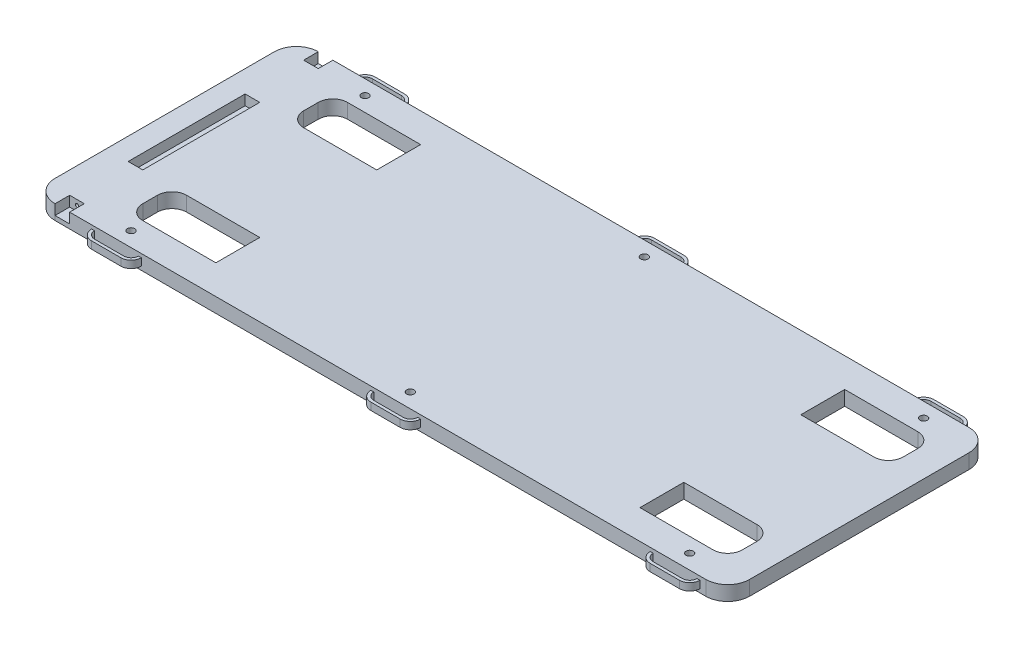
SolidWorks part; units mm, degrees
ref_plane "Front Plane" through (0, 0, 0) normal (0, 0, 1) x (1, 0, 0)
ref_plane "Top Plane" through (0, 0, 0) normal (0, 1, 0) x (1, 0, 0)
ref_plane "Right Plane" through (0, 0, 0) normal (1, 0, 0) x (0, 0, -1)
sketch "Main Body" plane through (0, 0, 0) normal (0, 1, 0) x (1, 0, 0)
  line L0 (-301.625, -95.25) -> (-301.625, 95.25)
  line L1 (-282.575, 114.3) -> (282.575, 114.3)
  line L2 (-282.575, -114.3) -> (282.575, -114.3)
  line L3 (301.625, 95.25) -> (301.625, -95.25)
  line L4 (-301.625, 0) -> (301.625, 0) construction
  arc A0 (-301.625, 95.25) -> (-282.575, 114.3) centre (-282.575, 95.25) cw
  arc A1 (-282.575, -114.3) -> (-301.625, -95.25) centre (-282.575, -95.25) cw
  arc A2 (282.575, 114.3) -> (301.625, 95.25) centre (282.575, 95.25) cw
  arc A3 (301.625, -95.25) -> (282.575, -114.3) centre (282.575, -95.25) cw
  point P14 (0, 0)
  dimension "D3" = 19.05
  dimension "D1" = 228.6
  dimension "D2" = 603.25
extrude "Boss-Extrude1" add sketch "Main Body" along normal blind 12.7
sketch "Sketch2" plane through (0, 0, 114.3) normal (0, 0, 1) x (1, 0, 0)
  line L0 (-282.575, 0) -> (282.575, 0) construction
  line L1 (-282.575, 12.7) -> (-260.35, 12.7)
  line L3 (-273.05, 0) -> (-260.35, 0)
sketch "Backrest Bracket Slot" plane through (0, 0, 114.3) normal (0, 0, 1) x (1, 0, 0)
  line L1 (-282.575, 12.7) -> (-269.875, 12.7)
  line L2 (-282.575, 12.7) -> (-282.575, 3.81)
  line L3 (-282.575, 3.81) -> (-269.875, 3.81)
  line L4 (-269.875, 12.7) -> (-269.875, 3.81)
  dimension "D1" = 12.7
  dimension "D2" = 8.89
extrude "Cut-Extrude3" cut sketch "Backrest Bracket Slot" against normal blind 12.7
sketch "Backrest Screw Hole" plane through (0, 0, 101.6) normal (0, 0, 1) x (1, 0, 0)
  line L0 (-282.575, 8.255) -> (-269.875, 8.255) construction
  line L1 (-282.575, 12.7) -> (-282.575, 3.81) construction
  line L2 (-269.875, 3.81) -> (-269.875, 12.7) construction
  circle A0 centre (-276.225, 8.255) radius 1.397
  dimension "D1" = 2.794
extrude "Cut-Extrude4" cut sketch "Backrest Screw Hole" against normal blind 6.35
mirror "Mirror1" about plane through (0, 0, 0) normal (0, 0, 1) of "Cut-Extrude4", "Cut-Extrude3"
sketch "Couch Foot Slits" plane through (0, 12.7, 0) normal (0, 1, 0) x (1, 0, 0)
  line L0 (-269.875, 101.6) -> (-269.875, -101.6) construction
  line L1 (-231.775, 88.9) -> (-168.275, 88.9)
  line L2 (-231.775, 50.8) -> (-168.275, 50.8)
  line L3 (-244.475, 76.2) -> (-244.475, 63.5)
  line L4 (276.225, 76.2) -> (276.225, 63.5)
  line L5 (-231.775, -50.8) -> (-168.275, -50.8)
  line L6 (-231.775, -88.9) -> (-168.275, -88.9)
  line L7 (-244.475, -63.5) -> (-244.475, -76.2)
  line L8 (276.225, -63.5) -> (276.225, -76.2)
  line L9 (301.625, -95.25) -> (301.625, 95.25) construction
  line L10 (282.575, 114.3) -> (-269.875, 114.3) construction
  line L12 (-269.875, -114.3) -> (282.575, -114.3) construction
  line L14 (200.025, 88.9) -> (263.525, 88.9)
  line L16 (-168.275, 88.9) -> (-168.275, 50.8)
  line L18 (200.025, 88.9) -> (200.025, 50.8)
  line L20 (-168.275, -50.8) -> (-168.275, -88.9)
  line L22 (200.025, -50.8) -> (200.025, -88.9)
  line L23 (200.025, 50.8) -> (263.525, 50.8)
  line L24 (200.025, -50.8) -> (263.525, -50.8)
  line L25 (200.025, -88.9) -> (263.525, -88.9)
  arc A0 (-244.475, 76.2) -> (-231.775, 88.9) centre (-231.775, 76.2) cw
  arc A1 (-231.775, 50.8) -> (-244.475, 63.5) centre (-231.775, 63.5) cw
  arc A2 (263.525, 88.9) -> (276.225, 76.2) centre (263.525, 76.2) cw
  arc A3 (276.225, 63.5) -> (263.525, 50.8) centre (263.525, 63.5) cw
  arc A4 (-244.475, -63.5) -> (-231.775, -50.8) centre (-231.775, -63.5) cw
  arc A5 (-231.775, -88.9) -> (-244.475, -76.2) centre (-231.775, -76.2) cw
  arc A6 (263.525, -50.8) -> (276.225, -63.5) centre (263.525, -63.5) cw
  arc A7 (276.225, -76.2) -> (263.525, -88.9) centre (263.525, -76.2) cw
  dimension "D6" = 12.7
  dimension "D9" = 12.7
  dimension "D1" = 25.4
  dimension "D2" = 25.4
  dimension "D3" = 25.4
  dimension "D4" = 25.4
  dimension "D5" = 101.6
  dimension "D7" = 76.2
  dimension "D8" = 76.2
extrude "Cut-Extrude5" cut sketch "Couch Foot Slits" against normal blind 25.4
ref_plane "Central Plane" through (0, 6.35, 0) normal (0, 1, 0) x (1, 0, 0)
sketch "Sketch24" plane through (0, 6.35, 0) normal (0, 1, 0) x (1, 0, 0)
  line L0 (-269.875, -114.3) -> (282.575, -114.3) construction
  line L1 (0.635, -120.65) -> (26.035, -120.65)
  line L2 (-248.285, -114.3) -> (-248.285, -101.5898) construction
  line L3 (-241.935, -120.65) -> (-216.535, -120.65)
  line L5 (-241.935, -123.19) -> (-216.535, -123.19)
  line L7 (-250.825, -114.3) -> (-248.285, -114.3)
  line L8 (-210.185, -114.3) -> (-207.645, -114.3)
  line L9 (32.385, -114.3) -> (34.925, -114.3)
  line L10 (0.635, -123.19) -> (26.035, -123.19)
  line L11 (-8.255, -114.3) -> (-5.715, -114.3)
  line L12 (243.205, -120.65) -> (268.605, -120.65)
  line L13 (274.955, -114.3) -> (277.495, -114.3)
  line L14 (243.205, -123.19) -> (268.605, -123.19)
  line L15 (234.315, -114.3) -> (236.855, -114.3)
  line L16 (-241.935, -120.65) -> (0.635, -120.65) construction
  arc A0 (-241.935, -120.65) -> (-248.285, -114.3) centre (-241.935, -114.3) cw
  arc A1 (-241.935, -123.19) -> (-250.825, -114.3) centre (-241.935, -114.3) cw
  arc A2 (-216.535, -123.19) -> (-207.645, -114.3) centre (-216.535, -114.3) ccw
  arc A3 (-216.535, -120.65) -> (-210.185, -114.3) centre (-216.535, -114.3) ccw
  arc A4 (26.035, -120.65) -> (32.385, -114.3) centre (26.035, -114.3) ccw
  arc A5 (26.035, -123.19) -> (34.925, -114.3) centre (26.035, -114.3) ccw
  arc A6 (0.635, -123.19) -> (-8.255, -114.3) centre (0.635, -114.3) cw
  arc A7 (0.635, -120.65) -> (-5.715, -114.3) centre (0.635, -114.3) cw
  arc A8 (268.605, -120.65) -> (274.955, -114.3) centre (268.605, -114.3) ccw
  arc A9 (268.605, -123.19) -> (277.495, -114.3) centre (268.605, -114.3) ccw
  arc A10 (243.205, -123.19) -> (234.315, -114.3) centre (243.205, -114.3) cw
  arc A11 (243.205, -120.65) -> (236.855, -114.3) centre (243.205, -114.3) cw
  dimension "D2" = 2.54
  dimension "D1" = 2.54
  dimension "D3" = 38.1
  dimension "D4" = 25.4
  dimension "D5" = 19.05
  dimension "D7" = 242.57
  dimension "D6" = 3
extrude "Boss-Extrude2" add sketch "Sketch24" along normal mid plane 6.35
mirror "Mirror2" about plane through (0, 0, 0) normal (0, 0, 1) of "Boss-Extrude2"
sketch "Sketch37" plane through (0, 12.7, 0) normal (0, 1, 0) x (1, 0, 0)
  line L0 (-282.575, 101.6) -> (-282.575, 114.3) construction
  line L1 (-282.575, 50.8) -> (-269.875, 50.8)
  line L2 (-282.575, 50.8) -> (-282.575, -50.8)
  line L3 (-282.575, -50.8) -> (-269.875, -50.8)
  line L4 (-269.875, 50.8) -> (-269.875, -50.8)
  line L5 (-269.875, 101.6) -> (-269.875, 114.3) construction
  line L6 (-276.225, 101.6) -> (-274.828, -101.6) construction
  line L7 (-269.875, 101.6) -> (-282.575, 101.6) construction
  point P13 (-269.875, 0)
  point P14 (-275.5265, 0)
  dimension "D1" = 101.6
extrude "Cut-Extrude7" cut sketch "Sketch37" against normal blind 8.89
sketch "Sketch38" plane through (0, 12.7, 0) normal (0, 1, 0) x (1, 0, 0)
  line L0 (-250.825, -114.3) -> (-207.645, -114.3) construction
  line L1 (-221.2987, -88.9) -> (-221.2987, -114.3) construction
  line L2 (-231.775, -88.9) -> (-168.275, -88.9) construction
  line L3 (-5.715, -114.3) -> (32.385, -114.3) construction
  line L4 (236.855, -114.3) -> (274.955, -114.3) construction
  circle A0 centre (-229.235, -101.6) radius 3.175
  circle A1 centre (13.335, -101.6) radius 3.175
  circle A2 centre (255.905, -101.6) radius 3.175
  point P6 (-229.235, -114.3)
  point P11 (-221.2987, -101.6)
  point P18 (13.335, -114.3)
  point P25 (255.905, -114.3)
  dimension "D1" = 6.35
extrude "Cut-Extrude8" cut sketch "Sketch38" against normal up to next (12.7 mm away)
mirror "Mirror3" about plane through (0, 0, 0) normal (0, 0, 1) of "Cut-Extrude8"
ref_point "Point1"
equation "\"0.4n\"=0.5"
